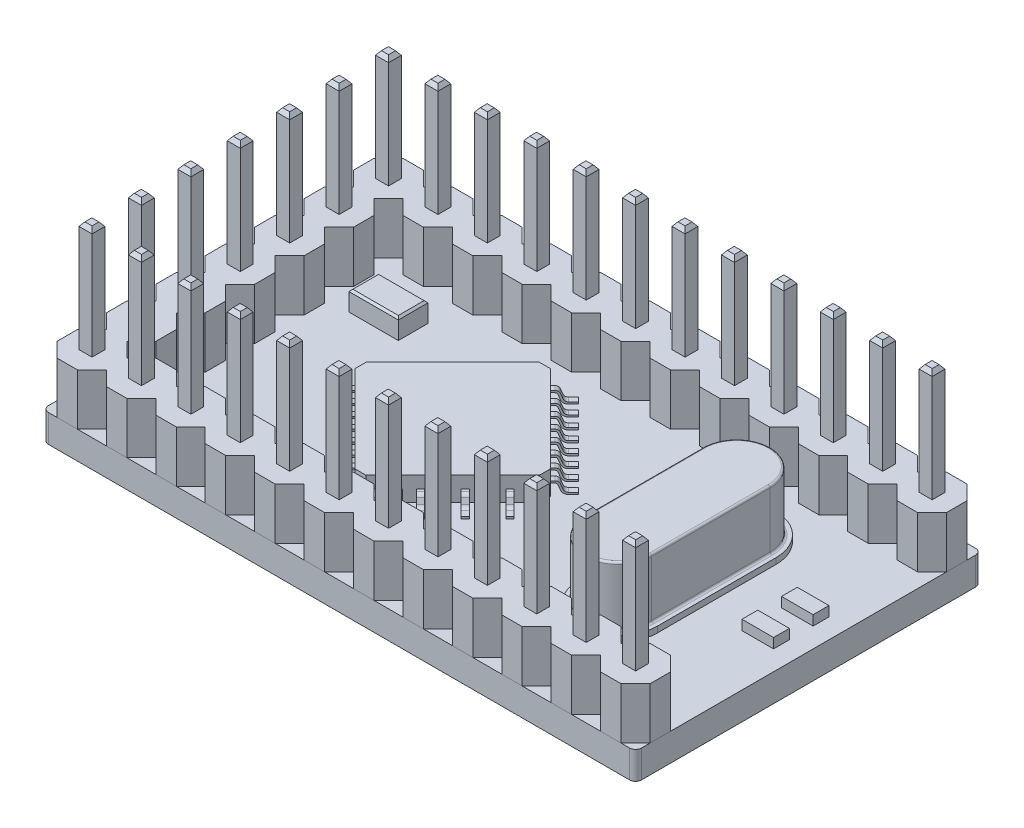
SolidWorks part; units mm, degrees
ref_plane "前视基准面" through (0, 0, 0) normal (0, 0, 1) x (1, 0, 0)
ref_plane "上视基准面" through (0, 0, 0) normal (0, 1, 0) x (1, 0, 0)
ref_plane "右视基准面" through (0, 0, 0) normal (1, 0, 0) x (0, 0, -1)
sketch "草图1" plane through (0, 0, 0) normal (0, 1, 0) x (1, 0, 0)
  line L1 (0, 0) -> (30, 0)
  line L2 (0, 0) -> (0, 17.5)
  line L3 (0, 17.5) -> (30, 17.5)
  line L4 (30, 0) -> (30, 17.5)
  dimension "D1" = 30
  dimension "D2" = 17.5
extrude "凸台-拉伸1" add sketch "草图1" along normal blind 1.4
sketch "草图2" plane through (0, 1.4, 0) normal (0, 1, 0) x (1, 0, 0)
  line L0 (30, 17.5) -> (0, 17.5) construction
  line L1 (2.5, 15.7322) -> (2.5, 16.7678)
  line L2 (2.5, 16.7678) -> (1.7678, 17.5)
  line L3 (1.7678, 17.5) -> (0.7322, 17.5)
  line L4 (0.7322, 17.5) -> (0, 16.7678)
  line L5 (0, 16.7678) -> (0, 15.7322)
  line L6 (0, 15.7322) -> (0.7322, 15)
  line L7 (0.7322, 15) -> (1.7678, 15)
  line L8 (1.7678, 15) -> (2.5, 15.7322)
  line L9 (0, 17.5) -> (0, 0) construction
  circle A0 centre (1.25, 16.25) radius 1.25 construction
  dimension "D1" = 2.5
extrude "凸台-拉伸2" add sketch "草图2" along normal blind 2.6 separate body
sketch "草图4" plane through (0, 4, 0) normal (0, 1, 0) x (1, 0, 0)
  line L1 (0.92, 16.575) -> (1.58, 16.575)
  line L2 (0.92, 16.575) -> (0.92, 15.925)
  line L3 (0.92, 15.925) -> (1.58, 15.925)
  line L4 (1.58, 16.575) -> (1.58, 15.925)
  line L5 (0.92, 16.575) -> (1.58, 15.925) construction
  line L6 (0.92, 15.925) -> (1.58, 16.575) construction
  line L8 (2.5, 15.7322) -> (2.5, 16.7678)
  line L9 (2.5, 16.7678) -> (1.7678, 17.5)
  line L10 (1.7678, 17.5) -> (0.7322, 17.5)
  line L11 (0.7322, 17.5) -> (0, 16.7678)
  line L12 (0, 16.7678) -> (0, 15.7322)
  line L13 (0, 15.7322) -> (0.7322, 15)
  line L14 (0.7322, 15) -> (1.7678, 15)
  line L15 (1.7678, 15) -> (2.5, 15.7322)
  line L16 (2.5, 15.7322) -> (2.5, 16.7678) construction
  line L17 (2.5, 16.7678) -> (1.7678, 17.5) construction
  line L18 (1.7678, 17.5) -> (0.7322, 17.5) construction
  line L19 (0.7322, 17.5) -> (0, 16.7678) construction
  line L20 (0, 16.7678) -> (0, 15.7322) construction
  line L21 (0, 15.7322) -> (0.7322, 15) construction
  line L22 (0.7322, 15) -> (1.7678, 15) construction
  line L23 (1.7678, 15) -> (2.5, 15.7322) construction
  circle A0 centre (1.25, 16.25) radius 1.25 construction
  dimension "D2" = 2.5
  dimension "D3" = 0.66
  dimension "D4" = 0.65
  dimension "D1" = 0
extrude "凸台-拉伸3" add sketch "草图4" along normal blind 5.6 separate body
chamfer "倒角1" distance 0.2 angle 37 4 edges at (1.25, 9.6, -15.925) (0.92, 9.6, -16.25) (1.25, 9.6, -16.575) (1.58, 9.6, -16.25)
pattern_linear "阵列(线性)3" count 12 spacing 2.5 along (1, 0, 0) count 2 spacing 15 along (0, 0, 1) of "凸台-拉伸2", "凸台-拉伸3", "倒角1"
sketch "草图7" plane through (0, 0, 0) normal (0, 0, 1) x (1, 0, 0)
  line L0 (0, 1.4) -> (30, 1.4)
split line "分割线1"
sketch "草图9" plane through (0, 1.4, 0) normal (0, 1, 0) x (1, 0, 0)
  line L0 (7.0503, 8.75) -> (12, 3.8003)
  line L1 (7.0503, 8.75) -> (12, 13.6997)
  line L2 (12, 3.8003) -> (16.9497, 8.75)
  line L3 (12, 13.6997) -> (16.9497, 8.75)
  line L4 (7.0503, 8.75) -> (16.9497, 8.75) construction
  line L5 (12, 3.8003) -> (12, 13.6997) construction
  line L6 (0, 8.75) -> (30, 8.75) construction
  line L7 (0, 15.7322) -> (0, 1.7678) construction
  line L8 (30, 1.7678) -> (30, 15.7322) construction
  point P1 (12, 8.75)
  dimension "D1" = 7
  dimension "D2" = 7
  dimension "D3" = 12
extrude "凸台-拉伸4" add sketch "草图9" along normal blind 1.2
chamfer "倒角2" distance 0.4 angle 45 4 edges at (12, 2, -3.8003) (7.0503, 2, -8.75) (12, 2, -13.6997) (16.9497, 2, -8.75)
ref_plane "基准面2" through (12.4963, 0, -12.4963) normal (0.7071, 0, -0.7071) x (-0.7071, 0, -0.7071)
sketch "草图12" plane through (12.4963, 0, -12.4963) normal (0.7071, 0, -0.7071) x (-0.7071, 0, -0.7071)
  line L0 (-5.7981, 2) -> (-5.9664, 2)
  line L1 (-5.7981, 2.6) -> (-5.7981, 1.4) construction
  line L2 (-6.1527, 1.8727) -> (-6.2484, 1.6273)
  line L3 (-6.4348, 1.5) -> (-6.7981, 1.5)
  line L4 (-6.7981, 1.5) -> (-6.7981, 1.4)
  line L5 (-7.5888, 1.4) -> (-6.5533, 1.4) construction
  line L6 (-5.7981, 1.9) -> (-5.9664, 1.9)
  line L7 (-6.0596, 1.8363) -> (-6.1553, 1.591)
  line L8 (-6.4348, 1.4) -> (-6.7981, 1.4)
  line L9 (-5.7981, 2) -> (-5.7981, 1.9)
  arc A0 (-5.9664, 2) -> (-6.1527, 1.8727) centre (-5.9664, 1.8) ccw
  arc A1 (-6.2484, 1.6273) -> (-6.4348, 1.5) centre (-6.4348, 1.7) cw
  arc A2 (-5.9664, 1.9) -> (-6.0596, 1.8363) centre (-5.9664, 1.8) ccw
  arc A3 (-6.1553, 1.591) -> (-6.4348, 1.4) centre (-6.4348, 1.7) cw
  point P11 (-6.1031, 2)
  point P14 (-6.2981, 1.5)
  dimension "D5" = 0.2
  dimension "D1" = 1
  dimension "D2" = 0.1
  dimension "D3" = 0.305
  dimension "D4" = 0.5
  dimension "D6" = 0.1
extrude "凸台-拉伸5" add sketch "草图12" against normal blind 0.3 contours A3 L7 A2 L6 L9 L0 A0 L2 A1 L3 L4 L8
pattern_linear "阵列(线性)4" count 8 spacing 0.8 along (-0.7071, 0, 0.7071) of "凸台-拉伸5"
ref_plane "基准面4" through (3.7463, 0, 3.7463) normal (0.7071, 0, 0.7071) x (0.7071, 0, -0.7071)
sketch "草图13" plane through (3.7463, 0, 3.7463) normal (0.7071, 0, 0.7071) x (0.7071, 0, -0.7071)
  line L0 (11.1725, 2) -> (11.0079, 2)
  line L1 (11.1725, 2.6) -> (11.1725, 1.4) construction
  line L2 (10.8222, 1.8743) -> (10.7228, 1.6257)
  line L3 (10.5371, 1.5) -> (10.1725, 1.5)
  line L4 (10.1725, 1.5) -> (10.1725, 1.4)
  line L5 (11.1244, 1.4) -> (1.25, 1.4) construction
  line L6 (11.1725, 1.9) -> (11.0079, 1.9)
  line L7 (10.915, 1.8371) -> (10.8156, 1.5886)
  line L8 (10.5371, 1.4) -> (10.1725, 1.4)
  line L9 (11.1725, 2) -> (11.1725, 1.9)
  arc A0 (11.0079, 2) -> (10.8222, 1.8743) centre (11.0079, 1.8) ccw
  arc A1 (10.7228, 1.6257) -> (10.5371, 1.5) centre (10.5371, 1.7) cw
  arc A2 (11.0079, 1.9) -> (10.915, 1.8371) centre (11.0079, 1.8) ccw
  arc A3 (10.8156, 1.5886) -> (10.5371, 1.4) centre (10.5371, 1.7) cw
  point P11 (10.8725, 2)
  point P14 (10.6725, 1.5)
  dimension "D5" = 0.2
  dimension "D1" = 0.1
  dimension "D2" = 1
  dimension "D3" = 0.3
  dimension "D4" = 0.5
  dimension "D6" = 0.1
extrude "凸台-拉伸6" add sketch "草图13" against normal blind 0.3 contours A3 L7 A2 L6 L9 L0 A0 L2 A1 L3 L4 L8
pattern_linear "阵列(线性)5" count 8 spacing 0.8 along (-0.7071, 0, -0.7071) of "凸台-拉伸6"
ref_plane "基准面5" through (10.375, 0, -10.375) normal (0.7071, 0, -0.7071) x (-0.7071, 0, -0.7071)
ref_plane "基准面6" through (1.625, 0, 1.625) normal (-0.7071, 0, -0.7071) x (-0.7071, 0, 0.7071)
mirror "镜向1" about plane through (10.375, 0, -10.375) normal (0.7071, 0, -0.7071) of "阵列(线性)5", "凸台-拉伸6"
mirror "镜向2" about plane through (1.625, 0, 1.625) normal (-0.7071, 0, -0.7071) of "阵列(线性)4", "凸台-拉伸5"
sketch "草图14" plane through (0, 1.4, 0) normal (0, 1, 0) x (1, 0, 0)
  line L0 (23.3625, 11.75) -> (23.3625, 5.75) construction
  line L1 (25.3625, 11.75) -> (25.3625, 5.75)
  line L2 (21.3625, 11.75) -> (21.3625, 5.75)
  line L3 (30, 8.75) -> (0, 8.75) construction
  line L4 (30, 1.7678) -> (30, 15.7322) construction
  line L5 (0, 15.7322) -> (0, 1.7678) construction
  arc A0 (25.3625, 11.75) -> (21.3625, 11.75) centre (23.3625, 11.75) ccw
  arc A1 (21.3625, 5.75) -> (25.3625, 5.75) centre (23.3625, 5.75) ccw
  point P2 (23.3625, 8.75)
  dimension "D2" = 2
  dimension "D1" = 6
extrude "凸台-拉伸7" add sketch "草图14" along normal blind 0.3
sketch "草图15" plane through (0, 1.7, 0) normal (0, 1, 0) x (1, 0, 0)
  line L4 (21.6625, 11.75) -> (21.6625, 5.75)
  line L5 (25.0625, 5.75) -> (25.0625, 11.75)
  line L6 (21.6625, 11.75) -> (21.6625, 5.75)
  line L7 (25.0625, 5.75) -> (25.0625, 11.75)
  arc A4 (25.0625, 11.75) -> (21.6625, 11.75) centre (23.3625, 11.75) ccw
  arc A5 (21.6625, 5.75) -> (25.0625, 5.75) centre (23.3625, 5.75) ccw
  arc A6 (25.0625, 11.75) -> (21.6625, 11.75) centre (23.3625, 11.75) ccw
  arc A7 (21.6625, 5.75) -> (25.0625, 5.75) centre (23.3625, 5.75) ccw
  dimension "D1" = 0.3
extrude "凸台-拉伸8" add sketch "草图15" along normal blind 3
fillet "圆角1" radius 0.1 4 edges at (23.3625, 1.7, -13.45) (25.0625, 1.7, -8.75) (23.3625, 1.7, -4.05) (21.6625, 1.7, -8.75)
fillet "圆角2" radius 0.1 4 edges at (23.3625, 4.7, -13.45) (25.0625, 4.7, -8.75) (23.3625, 4.7, -4.05) (21.6625, 4.7, -8.75)
pattern_linear "阵列(线性)6" count 6 spacing 2.5 along (0, 0, 1) of "凸台-拉伸2", "凸台-拉伸3", "倒角1"
sketch "草图16" plane through (0, 1.4, 0) normal (0, 1, 0) x (1, 0, 0)
  line L0 (5.7322, 17.5) -> (4.2678, 17.5) construction
  line L1 (3.5, 13.5) -> (6, 13.5)
  line L2 (3.5, 13.5) -> (3.5, 12)
  line L3 (3.5, 12) -> (6, 12)
  line L4 (6, 13.5) -> (6, 12)
  line L5 (0, 13.2322) -> (0, 11.7678) construction
  dimension "D1" = 1.5
  dimension "D2" = 2.5
  dimension "D3" = 4
  dimension "D4" = 3.5
extrude "凸台-拉伸9" add sketch "草图16" along normal blind 1
chamfer "倒角3" distance 0.1 angle 45 4 edges at (3.5, 2.4, -12.75) (4.75, 2.4, -13.5) (6, 2.4, -12.75) (4.75, 2.4, -12)
sketch "草图17" plane through (0, 1.4, 0) normal (0, 1, 0) x (1, 0, 0)
  line L0 (30, 1.7678) -> (30, 15.7322) construction
  line L1 (27.4, 10.7821) -> (29, 10.7821)
  line L2 (27.4, 10.7821) -> (27.4, 9.9821)
  line L3 (27.4, 9.9821) -> (29, 9.9821)
  line L4 (29, 10.7821) -> (29, 9.9821)
  line L5 (27.4, 8.7821) -> (29, 8.7821)
  line L6 (27.4, 8.7821) -> (27.4, 7.9821)
  line L7 (27.4, 7.9821) -> (29, 7.9821)
  line L8 (29, 8.7821) -> (29, 7.9821)
  dimension "D1" = 1.6
  dimension "D2" = 0.8
  dimension "D3" = 1
  dimension "D4" = 2
extrude "凸台-拉伸10" add sketch "草图17" along normal blind 0.5
sketch "草图18" plane through (0, 0, 0) normal (-1, 0, 0) x (0, 0, 1)
  line L0 (-17.5, 1.4) -> (0, 1.4)
split line "分割线2"
fillet "圆角3" radius 0.3 4 edges at (0, 0.7, 0) (0, 0.7, -17.5) (30, 0.7, -17.5) (30, 0.7, 0)
